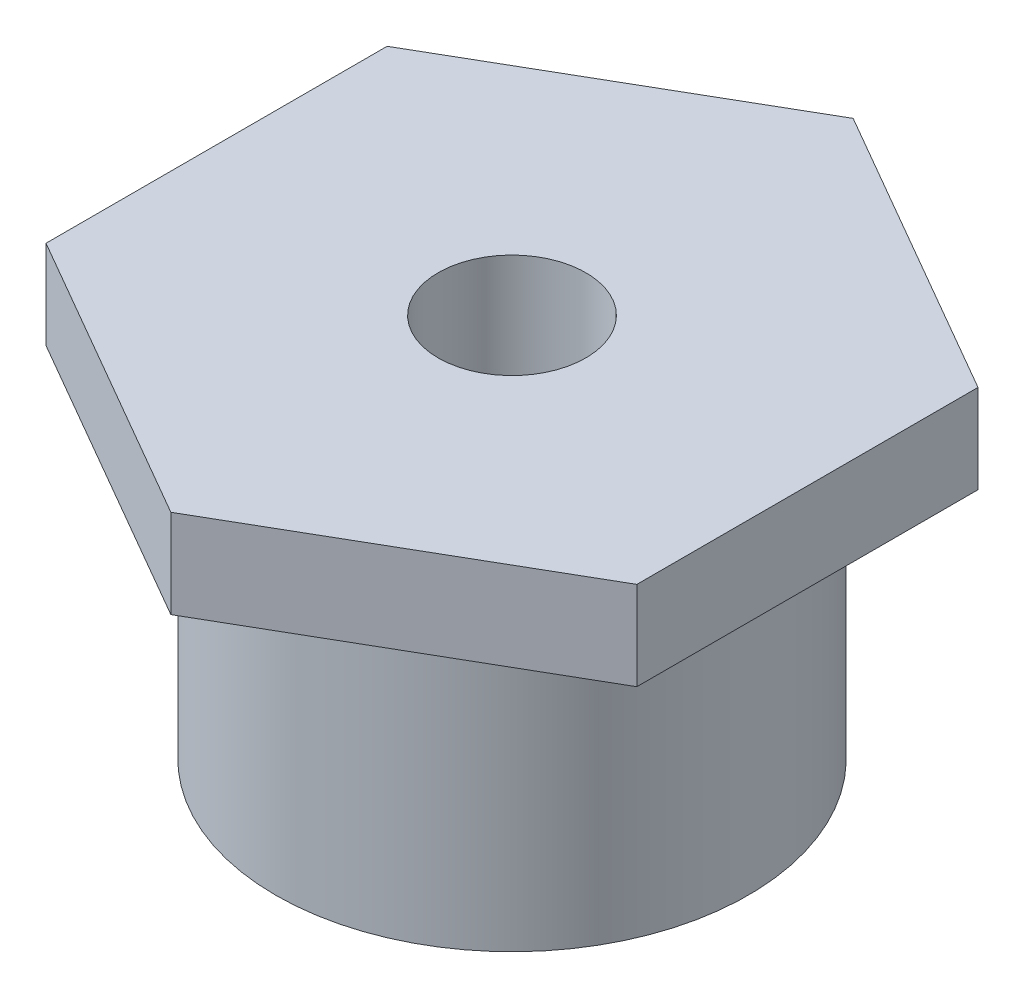
SolidWorks part; units mm, degrees
ref_plane "Front Plane" through (0, 0, 0) normal (0, 0, 1) x (1, 0, 0)
ref_plane "Top Plane" through (0, 0, 0) normal (0, 1, 0) x (1, 0, 0)
ref_plane "Right Plane" through (0, 0, 0) normal (1, 0, 0) x (0, 0, -1)
sketch "Sketch1" plane through (0, 0, 0) normal (0, 1, 0) x (1, 0, 0)
  circle A0 centre (0, 0) radius 40
  dimension "D1" = 80
extrude "Boss-Extrude1" add sketch "Sketch1" along normal blind 50
sketch "Sketch2" plane through (0, 50, 0) normal (0, 1, 0) x (1, 0, 0)
  line L1 (0, -57.735) -> (50, -28.8675)
  line L2 (50, -28.8675) -> (50, 28.8675)
  line L3 (50, 28.8675) -> (0, 57.735)
  line L4 (0, 57.735) -> (-50, 28.8675)
  line L5 (-50, 28.8675) -> (-50, -28.8675)
  line L6 (-50, -28.8675) -> (0, -57.735)
  circle A0 centre (0, 0) radius 50 construction
  dimension "D1" = 100
extrude "Boss-Extrude2" add sketch "Sketch2" along normal blind 15
sketch "Sketch4" plane through (0, 65, 0) normal (0, 1, 0) x (1, 0, 0)
  circle A0 centre (0, 0) radius 12.5
  dimension "D1" = 25
extrude "Cut-Extrude1" cut sketch "Sketch4" against normal blind 35
